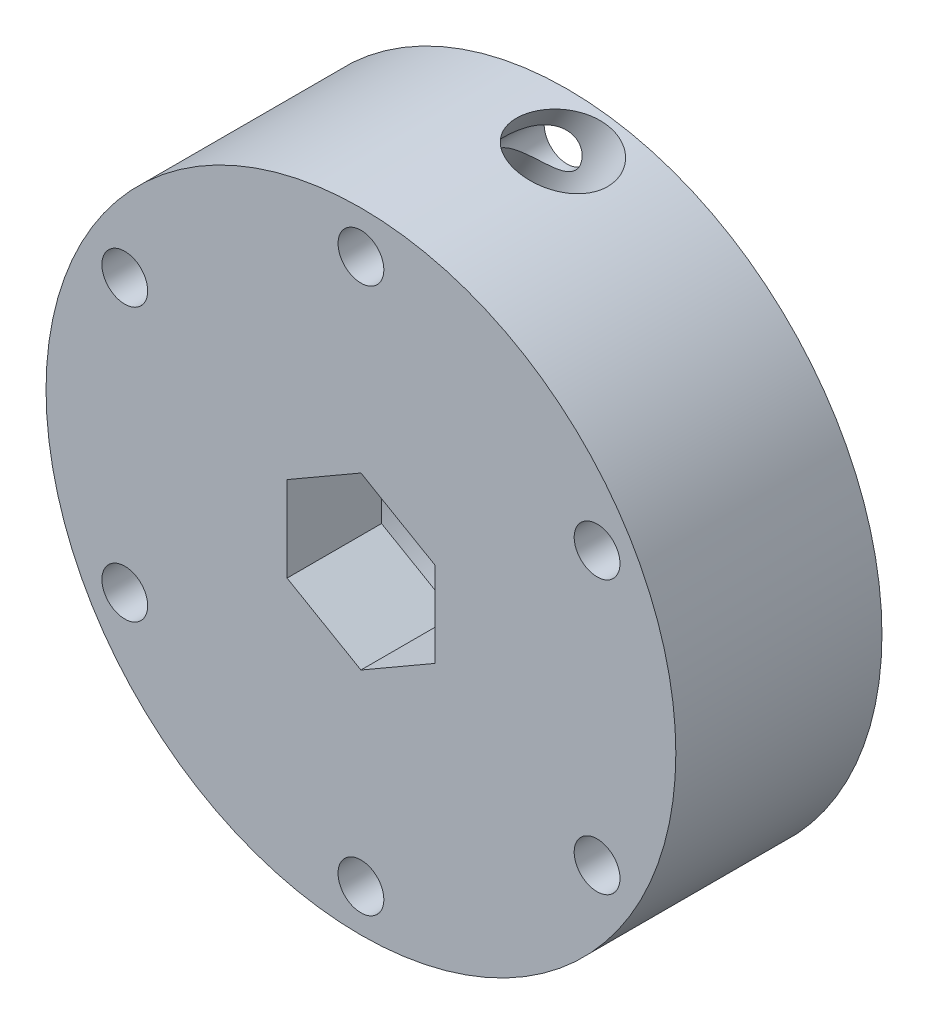
SolidWorks part; units mm, degrees
ref_plane "Front Plane" through (0, 0, 0) normal (0, 0, 1) x (1, 0, 0)
ref_plane "Top Plane" through (0, 0, 0) normal (0, 1, 0) x (1, 0, 0)
ref_plane "Right Plane" through (0, 0, 0) normal (1, 0, 0) x (0, 0, -1)
sketch "Sketch1" plane through (0, 0, 0) normal (0, 0, 1) x (1, 0, 0)
  circle A0 centre (0, 0) radius 27.5
  circle A1 centre (0, 23.8125) radius 2
  circle A2 centre (20.6222, 11.9063) radius 2
  circle A3 centre (20.6222, -11.9062) radius 2
  circle A4 centre (0, -23.8125) radius 2
  circle A5 centre (-20.6222, -11.9063) radius 2
  circle A6 centre (-20.6222, 11.9062) radius 2
  point P17 (0, 0)
  dimension "D1" = 55
  dimension "D2" = 23.8125
  dimension "D3" = 4
  dimension "D4" = 6
extrude "Boss-Extrude1" add sketch "Sketch1" along normal blind 18
sketch "Sketch2" plane through (0, 0, 0) normal (0, 0, -1) x (-1, 0, 0)
  line L13 (0, 7.4497) -> (-6.4516, 3.7248)
  line L14 (-6.4516, 3.7248) -> (-6.4516, -3.7248)
  line L15 (-6.4516, -3.7248) -> (0, -7.4497)
  line L16 (0, -7.4497) -> (6.4516, -3.7248)
  line L17 (6.4516, -3.7248) -> (6.4516, 3.7248)
  line L18 (6.4516, 3.7248) -> (0, 7.4497)
  circle A0 centre (0, 0) radius 6.4516 construction
  dimension "D1" = 12.9032
extrude "Cut-Extrude1" cut sketch "Sketch2" against normal through all
sketch "Sketch3" plane through (0, 0, 0) normal (0, 0, -1) x (-1, 0, 0)
  circle A0 centre (0, 0) radius 15.675
  dimension "D1" = 31.35
extrude "Cut-Extrude2" cut sketch "Sketch3" against normal blind 9.75
sketch "Sketch5" plane through (0.2257, 7.3194, 0) normal (-0.5, -0.866, 0) x (0.866, -0.5, 0)
  circle A0 centre (-6.5358, 4.426) radius 3.75
  dimension "D1" = 7.5
  dimension "D2" = 10
extrude "Cut-Extrude4" cut sketch "Sketch5" against normal through all
